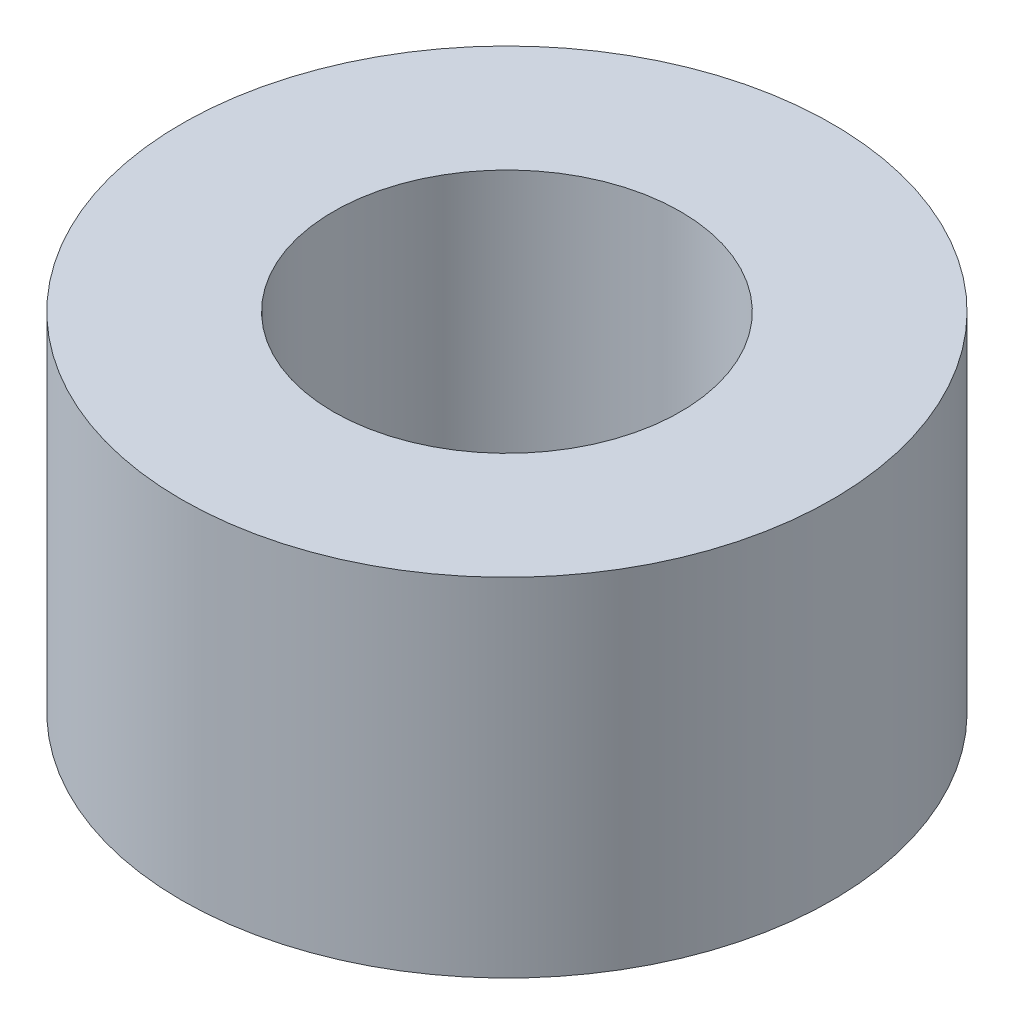
SolidWorks part; units mm, degrees
material "6061-T6 Al"
ref_plane "Front" through (0, 0, 0) normal (0, 0, 1) x (1, 0, 0)
ref_plane "Top" through (0, 0, 0) normal (0, 1, 0) x (1, 0, 0)
ref_plane "Right" through (0, 0, 0) normal (1, 0, 0) x (0, 0, -1)
sketch "Sketch1" plane through (0, 0, 0) normal (0, 1, 0) x (1, 0, 0)
  circle A0 centre (0, 0) radius 7.5
  dimension "D1" = 15
extrude "Boss-Extrude1" add sketch "Sketch1" along normal blind 8
sketch "Sketch2" plane through (0, 8, 0) normal (0, 1, 0) x (1, 0, 0)
  circle A0 centre (0, 0) radius 4
  dimension "D1" = 8
extrude "Cut-Extrude1" cut sketch "Sketch2" against normal blind 6
sketch "Sketch3" plane through (0, 0, 0) normal (0, -1, 0) x (1, 0, 0)
  circle A0 centre (0, 0) radius 1.075
  dimension "D1" = 2.15
extrude "Cut-Extrude2" cut sketch "Sketch3" against normal blind 6
